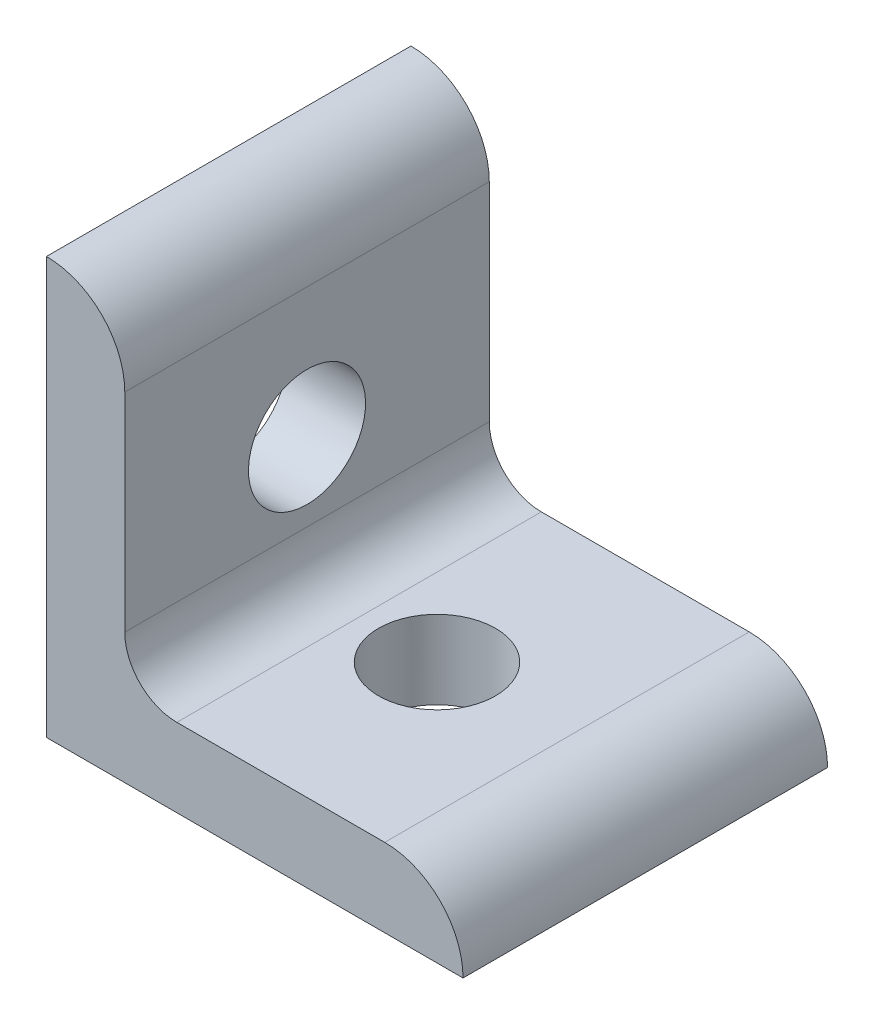
SolidWorks part; units mm, degrees
ref_plane "Front Plane" through (0, 0, 0) normal (0, 0, 1) x (1, 0, 0)
ref_plane "Top Plane" through (0, 0, 0) normal (0, 1, 0) x (1, 0, 0)
ref_plane "Right Plane" through (0, 0, 0) normal (1, 0, 0) x (0, 0, -1)
sketch "Sketch1" plane through (0, 0, 0) normal (0, 0, 1) x (1, 0, 0)
  line L0 (0, 0) -> (0, 25.4)
  line L1 (4.7752, 20.6248) -> (4.7752, 25.4) construction
  line L2 (4.7752, 20.6248) -> (4.7752, 7.9502)
  line L3 (7.9502, 4.7752) -> (20.6248, 4.7752)
  line L4 (4.7752, 25.4) -> (0, 25.4) construction
  line L5 (25.4, 0) -> (0, 0)
  line L6 (20.6248, 4.7752) -> (25.4, 4.7752) construction
  line L7 (25.4, 4.7752) -> (25.4, 0) construction
  arc A0 (4.7752, 20.6248) -> (0, 25.4) centre (0, 20.6248) ccw
  arc A1 (25.4, 0) -> (20.6248, 4.7752) centre (20.6248, 0) ccw
  arc A2 (4.7752, 7.9502) -> (7.9502, 4.7752) centre (7.9502, 7.9502) ccw
  point P10 (4.7752, 23.0124)
  dimension "E" = 3.175
  dimension "D" = 4.7752
  dimension "C" = 25.4
  dimension "B" = 25.4
extrude "Boss-Extrude1" add sketch "Sketch1" along normal mid plane 22.225
sketch "Sketch2" plane through (0, 0, 0) normal (0, 1, 0) x (1, 0, 0)
  line L0 (0, 0) -> (12.7, 0) construction
  circle A0 centre (12.7, 0) radius 3.5687
extrude "Cut-Extrude1" cut sketch "Sketch2" along normal through all
sketch "Sketch3" plane through (0, 0, 0) normal (1, 0, 0) x (0, 0, -1)
  line L0 (0, 0) -> (0, 12.7) construction
  circle A0 centre (0, 12.7) radius 3.5687
  dimension "D1" = 12.7
extrude "Cut-Extrude2" cut sketch "Sketch3" along normal through all
equation "\"E@Sketch3\" = \"E@Sketch2\""
equation "\"D1@Sketch3\" = \"D1@Sketch2\""
